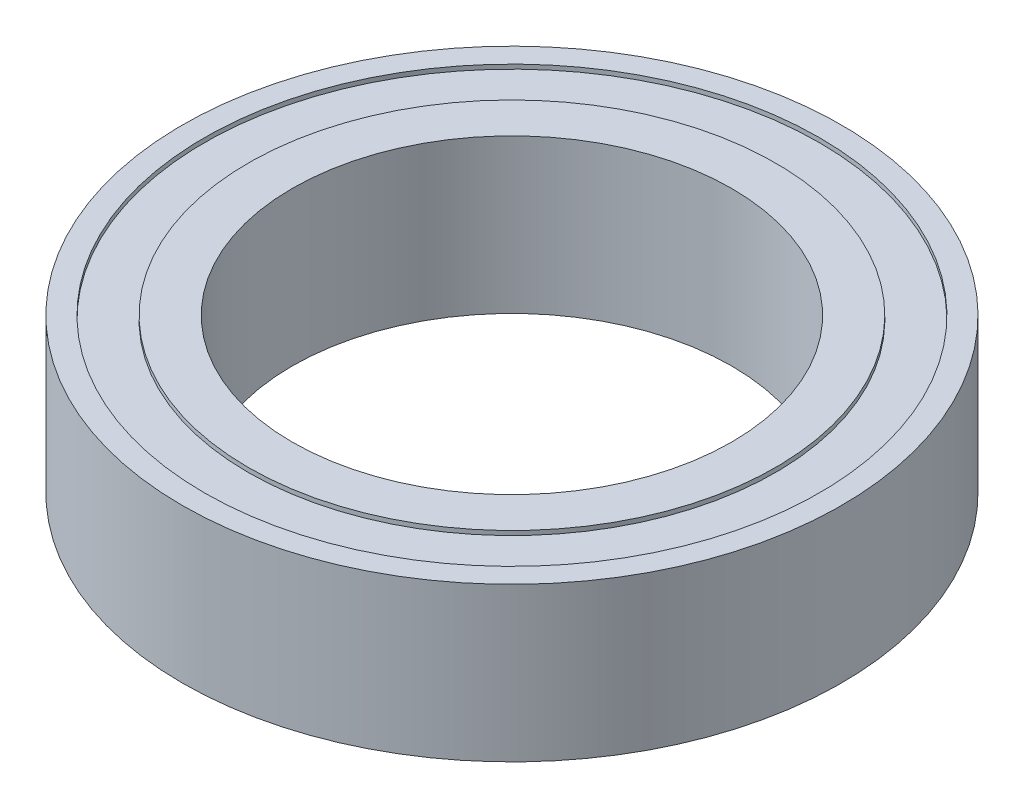
SolidWorks part; units mm, degrees
ref_plane "Front Plane" through (0, 0, 0) normal (0, 0, 1) x (1, 0, 0)
ref_plane "Top Plane" through (0, 0, 0) normal (0, 1, 0) x (1, 0, 0)
ref_plane "Right Plane" through (0, 0, 0) normal (1, 0, 0) x (0, 0, -1)
sketch "Sketch1" plane through (0, 0, 0) normal (0, 1, 0) x (1, 0, 0)
  circle A0 centre (0, 0) radius 7.5
  circle A1 centre (0, 0) radius 7
extrude "Boss-Extrude1" add sketch "Sketch1" along normal blind 3.5
sketch3d " "
  circle A1 centre (0, 0.1, 0) radius 7
  circle A2 centre (0, 0.1, 0) radius 6
  point P1 (0, 6.1, 0)
  point P6 (0, 7.1, 0)
  dimension "D2" = 14
  dimension "D3" = 12
  dimension "D1" = 0.1
sketch "Sketch6" plane through (0, 0.1, 0) normal (0, 1, 0) x (1, 0, 0)
  circle A0 centre (0, 0) radius 6
  circle A1 centre (0, 0) radius 7
extrude "Boss-Extrude4" add sketch "Sketch6" along normal blind 3.3
sketch "Sketch7" plane through (0, 0, 0) normal (0, 1, 0) x (1, 0, 0)
  circle A0 centre (0, 0) radius 6
  circle A1 centre (0, 0) radius 5
extrude "Boss-Extrude5" add sketch "Sketch7" along normal blind 3.5
